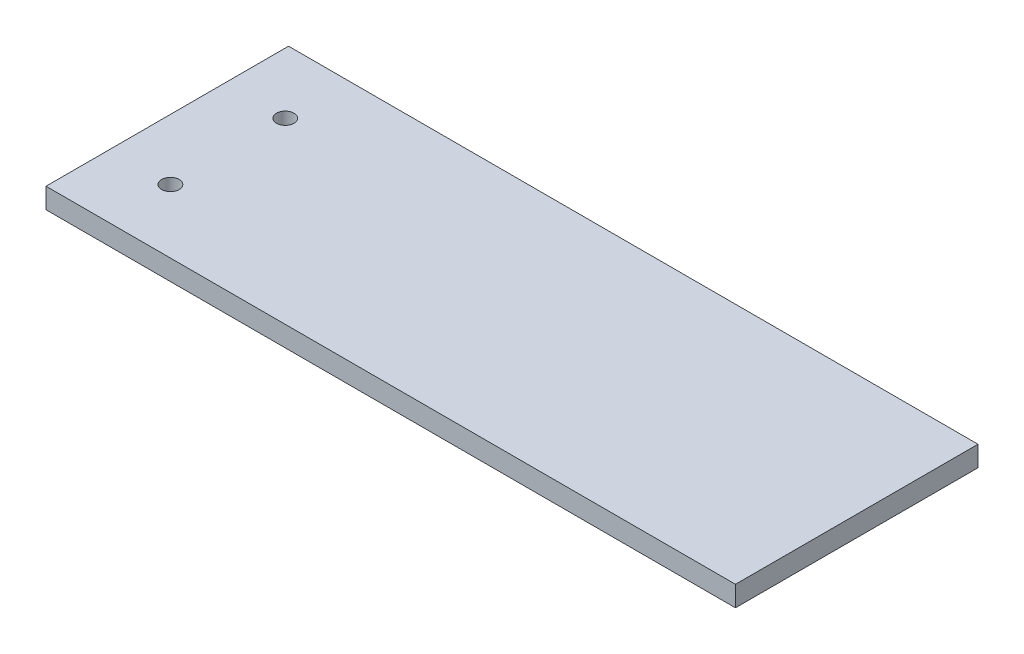
SolidWorks part; units mm, degrees
ref_plane "Front Plane" through (0, 0, 0) normal (0, 0, 1) x (1, 0, 0)
ref_plane "Top Plane" through (0, 0, 0) normal (0, 1, 0) x (1, 0, 0)
ref_plane "Right Plane" through (0, 0, 0) normal (1, 0, 0) x (0, 0, -1)
sketch "Sketch1" plane through (0, 0, 0) normal (0, 1, 0) x (1, 0, 0)
  line L1 (-22.7105, -14.0633) -> (193.546, -14.0633)
  line L2 (-22.7105, -14.0633) -> (-22.7105, 62.0146)
  line L3 (-22.7105, 62.0146) -> (193.546, 62.0146)
  line L4 (193.546, -14.0633) -> (193.546, 62.0146)
  point P4 (-22.7105, 62.0146)
extrude "Boss-Extrude1" add sketch "Sketch1" along normal blind 6.4
sketch "Sketch2" plane through (0, 0, 0) normal (0, -1, 0) x (1, 0, 0)
  circle A0 centre (-3.6605, -5.9146) radius 2.75
  circle A1 centre (-3.6605, -41.9146) radius 2.75
extrude "Cut-Extrude1" cut sketch "Sketch2" against normal blind 10
